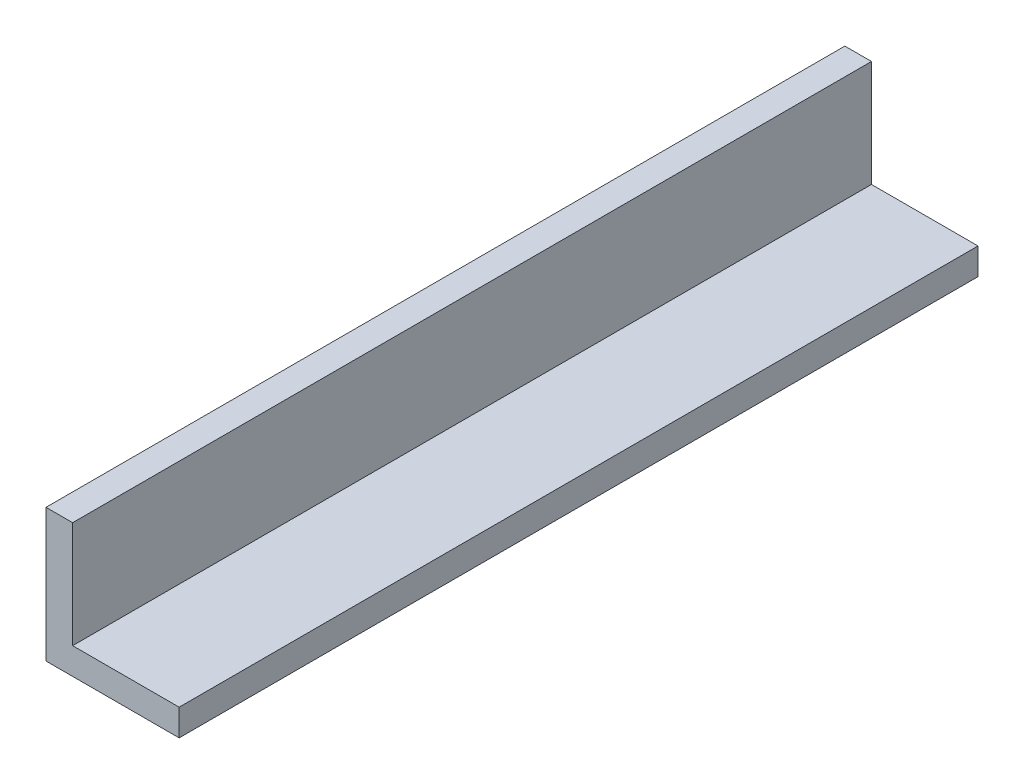
SolidWorks part; units mm, degrees
material "6061-T6 (SS)"
ref_plane "Front Plane" through (0, 0, 0) normal (0, 0, 1) x (1, 0, 0)
ref_plane "Top Plane" through (0, 0, 0) normal (0, 1, 0) x (1, 0, 0)
ref_plane "Right Plane" through (0, 0, 0) normal (1, 0, 0) x (0, 0, -1)
sketch "Sketch1" plane through (0, 0, 0) normal (0, 0, 1) x (1, 0, 0)
  line L0 (-1.27, 5.08) -> (-1.27, -1.27)
  line L1 (-1.27, -1.27) -> (5.08, -1.27)
  line L2 (5.08, -1.27) -> (5.08, 0)
  line L3 (5.08, 0) -> (0, 0)
  line L4 (0, 0) -> (0, 5.08)
  line L5 (0, 5.08) -> (-1.27, 5.08)
  dimension "D1" = 1.27
  dimension "D2" = 6.35
extrude "Boss-Extrude1" add sketch "Sketch1" along normal mid plane 38.1 contours L3 L4 L5 L0 L1 L2
